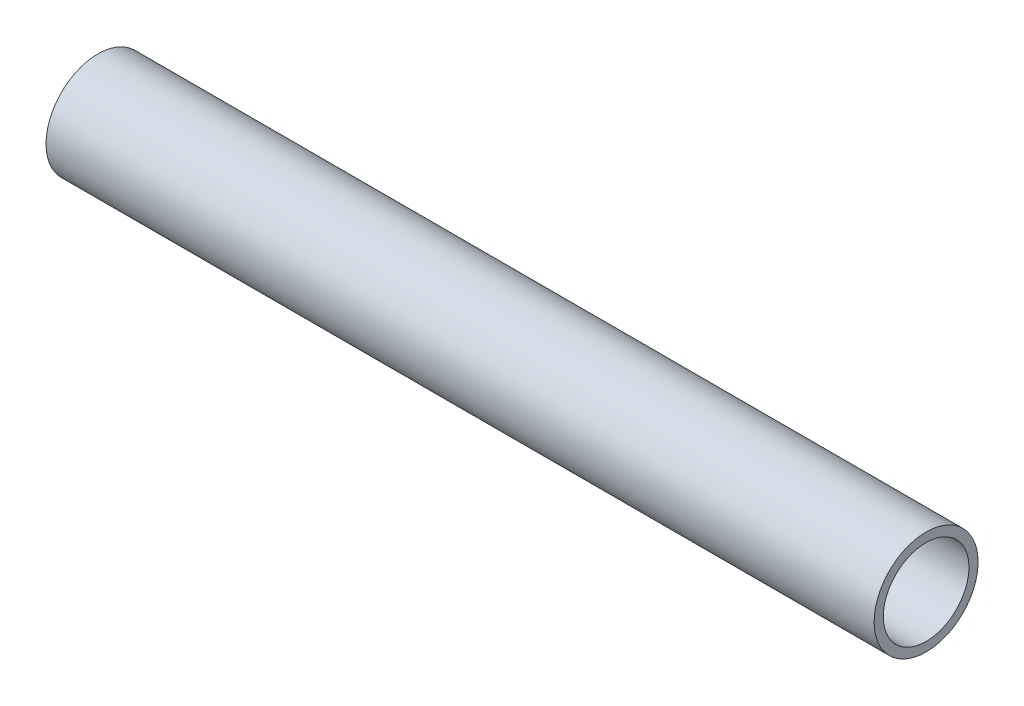
SolidWorks part; units mm, degrees
ref_plane "Front Plane" through (0, 0, 0) normal (0, 0, 1) x (1, 0, 0)
ref_plane "Top Plane" through (0, 0, 0) normal (0, 1, 0) x (1, 0, 0)
ref_plane "Right Plane" through (0, 0, 0) normal (1, 0, 0) x (0, 0, -1)
sketch "Sketch2" plane through (0, 0, 0) normal (0, 0, 1) x (1, 0, 0)
  line L1 (-104.1286, 675.7227) -> (-154.7004, 675.7227)
other "Pipe 0.5 SCH 40(1)"
ref_plane "Plane1" through (-104.1286, 675.7227, 0) normal (-1, 0, 0) x (0, -1, 0)
sketch "Sketch1" plane through (-104.1286, 675.7227, 0) normal (-1, 0, 0) x (0, -1, 0)
  circle A0 centre (0, 0) radius 2.6162
  circle A1 centre (0, 0) radius 3.175
  point P5 (0, 0)
  dimension "In_dia" = 5.2324
  dimension "Out_dia" = 6.35
